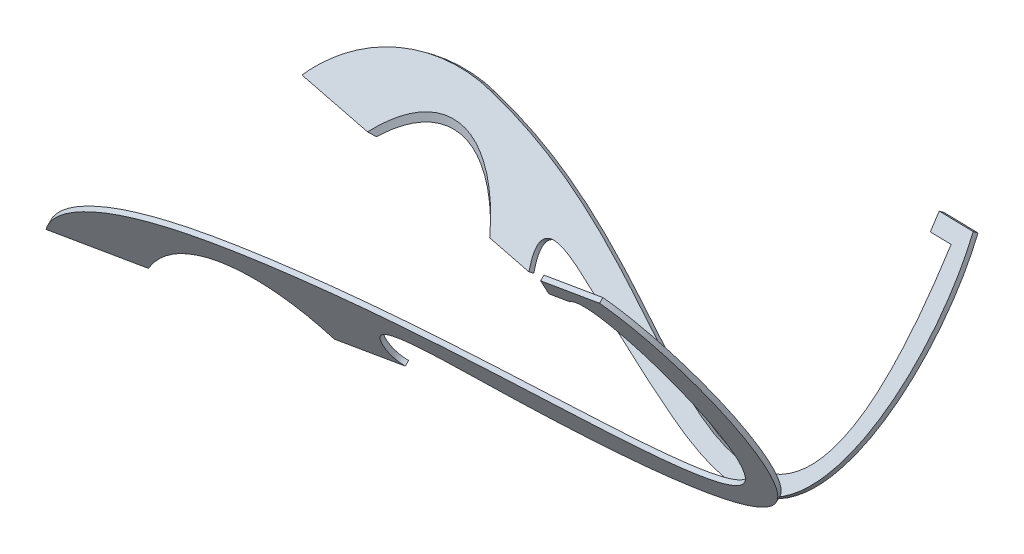
SolidWorks part; units mm, degrees
ref_plane "Front Plane" through (0, 0, 0) normal (0, 0, 1) x (1, 0, 0)
ref_plane "Top Plane" through (0, 0, 0) normal (0, 1, 0) x (1, 0, 0)
ref_plane "Right Plane" through (0, 0, 0) normal (1, 0, 0) x (0, 0, -1)
sketch "Sketch1" plane through (0, 0, 0) normal (0, 1, 0) x (1, 0, 0)
  line L0 (0, 0) -> (914.6295, 0) construction
  line L1 (-128.6663, 214.3478) -> (914.6295, 0) construction
  line L2 (914.6295, 0) -> (-128.6663, -214.3478) construction
  circle A0 centre (0, 0) radius 250
  dimension "D3" = 500
sketch "Sketch2" plane through (0, 0, 0) normal (0, 0, 1) x (1, 0, 0)
  line L0 (914.6295, 0) -> (914.6295, 405) construction
  line L1 (914.6295, 405) -> (-250, 405) construction
  line L2 (-250, 405) -> (-250, 0) construction
  line L3 (250, 0) -> (-250, 0) construction
  line L5 (0, 0) -> (-250, 0) construction
  line L6 (-250, 155) -> (0, 405) construction
  dimension "D1" = 250
  dimension "D2" = 405
  dimension "D3" = 45
ref_plane "Plane1" through (0, 405, 0) normal (0, 1, 0) x (-1, 0, 0)
sketch "Sketch3" plane through (0, 405, 0) normal (0, 1, 0) x (-1, 0, 0)
  line L0 (128.6663, 214.3478) -> (-790.8758, 214.3478) construction
  line L1 (-790.8758, 214.3478) -> (-914.6295, 0) construction
  line L2 (128.6663, -214.3478) -> (-1038.3833, -214.3478) construction
  line L3 (-1038.3833, -214.3478) -> (-914.6295, 0) construction
  line L4 (0, 250) -> (0, -250)
  line L5 (0, 250) -> (-770.292, 250)
  line L6 (-770.292, 250) -> (-790.8758, 214.3478)
  line L7 (0, -250) -> (-1058.9671, -250)
  line L8 (-1058.9671, -250) -> (-1038.3833, -214.3478)
  circle A0 centre (0, 0) radius 250 construction
  dimension "D1" = 120
ref_plane "Plane2" through (25.4161, -85.4208, -123.7077) normal (0.1667, -0.5603, -0.8114) x (-0.986, -0.0947, -0.1372)
sketch "Sketch4" plane through (25.4161, -85.4208, -123.7077) normal (0.1667, -0.5603, -0.8114) x (-0.986, -0.0947, -0.1372)
  line L0 (317.3223, 104.9383) -> (317.1821, 333.172)
  line L1 (317.3223, 104.9383) -> (-1200.9097, -98.9587)
  line L2 (-1200.9097, -98.9587) -> (-1200.9097, 500.3865)
  line L3 (-1200.9097, 500.3865) -> (-846.5591, 500.3865)
  line L4 (-846.5591, 500.3865) -> (-846.5591, 176.8828)
  line L5 (-846.5591, 176.8828) -> (317.1821, 333.172)
extrude "Boss-Extrude1" add sketch "Sketch4" along normal blind 10
ref_plane "Plane3" through (685.9722, 0, 396.0462) normal (-0.866, 0, -0.5) x (-0.5, 0, 0.866)
sketch "Sketch7" plane through (685.9722, 0, 396.0462) normal (-0.866, 0, -0.5) x (-0.5, 0, 0.866)
  line L3 (-457.3148, 0) -> (-457.3148, 405) construction
  ellipse E0 centre (-457.3148, 405) end of major axis (-457.3148, 760) minor radius 288.6751
  dimension "D1" = 355
  dimension "D2" = 50
sketch "Sketch8" plane through (25.4161, -85.4208, -123.7077) normal (-0.1667, 0.5603, 0.8114) x (0.9859, 0.1085, 0.1276)
  line L1 (-311.5508, 338.4437) -> (849.406, 162.6628) construction
  line L5 (-309.9114, 160.8393) -> (272.8346, 86.0257)
  line L6 (1040.2978, 437.6804) -> (991.2992, 437.6804)
  line L7 (991.2992, 437.6804) -> (991.2992, 470.324)
  line L8 (991.2992, 470.324) -> (1071.1946, 470.324)
  ellipse E0 centre (0, 0) end of major axis (-360.872, 36.61) minor radius 288.3377 (-309.9114, 160.8393) -> (29.1021, 286.8653) cw
  spline S0 degree 3 poles (29.1021, 286.8653) (182.9472, 265.0677) (564.8741, 132.4146) (1050.4277, -192.059) (1040.2978, 437.6804) knots 0 0 0 0 0.337701 1 1 1 1
  spline S1 degree 3 poles (272.8346, 86.0257) (243.6818, 172.7875) (445.5176, 96.2592) (611.6288, 25.9318) (1024.9184, -108.4261) (1099.6922, 306.775) (1071.1946, 470.324) knots 0 0 0 0 0.13386 0.347767 0.574791 1 1 1 1
extrude "Cut-Extrude3" cut sketch "Sketch8" against normal blind 10 flip side to cut
ref_plane "Plane4" through (28.8498, -76.3976, 140.4206) normal (0.1776, -0.4703, 0.8644) x (0.984, 0.0751, -0.1613)
sketch "Sketch9" plane through (28.8498, -76.3976, 140.4206) normal (0.1776, -0.4703, 0.8644) x (0.984, 0.0751, -0.1613)
  line L0 (-161.1927, 100.6482) -> (286.8671, 62.3901)
  line L1 (900.0331, 10.0342) -> (-161.1927, 100.6482) construction
  line L2 (-161.1927, 100.6482) -> (-326.0016, 114.7206)
  line L3 (748.0751, 483.6027) -> (712.4934, 486.6408)
  line L4 (712.4934, 486.6408) -> (712.4934, 522.5647)
  line L5 (712.4934, 522.5647) -> (813.0131, 513.9817)
  spline S0 degree 3 poles (-326.0016, 114.7206) (-290.6138, 180.7666) (-153.8485, 273.7533) (56.8903, 268.9734) (305.548, 213.9354) (518.0437, 127.6466) (1051.0659, -106.5016) (808.0622, 530.3516) (748.0751, 483.6027) knots 0 0 0 0 0.124854 0.265737 0.349321 0.553049 0.735068 1 1 1 1
  spline S1 degree 3 poles (286.8671, 62.3901) (265.5453, 75.3959) (255.1258, 200.915) (584.4092, 9.2054) (1075.1263, -132.9853) (913.1571, 415.2121) (813.0131, 513.9817) knots 0 0 0 0 0.058612 0.210636 0.58985 1 1 1 1
extrude "Boss-Extrude2" add sketch "Sketch9" along normal blind 10 separate body
sketch "Sketch6" plane through (0, 0, 0) normal (0, 1, 0) x (1, 0, 0)
  circle A0 centre (0, 0) radius 250
extrude "Cut-Extrude4" cut sketch "Sketch6" against normal mid plane 1000
ref_plane "Plane5" through (-202.5, 202.5, 0) normal (0.7071, -0.7071, 0) x (0, 0, -1)
sketch "Sketch10" plane through (-202.5, 202.5, 0) normal (0.7071, -0.7071, 0) x (0, 0, -1)
  ellipse E0 centre (0, 286.3782) end of major axis (0, 639.9316) minor radius 250
